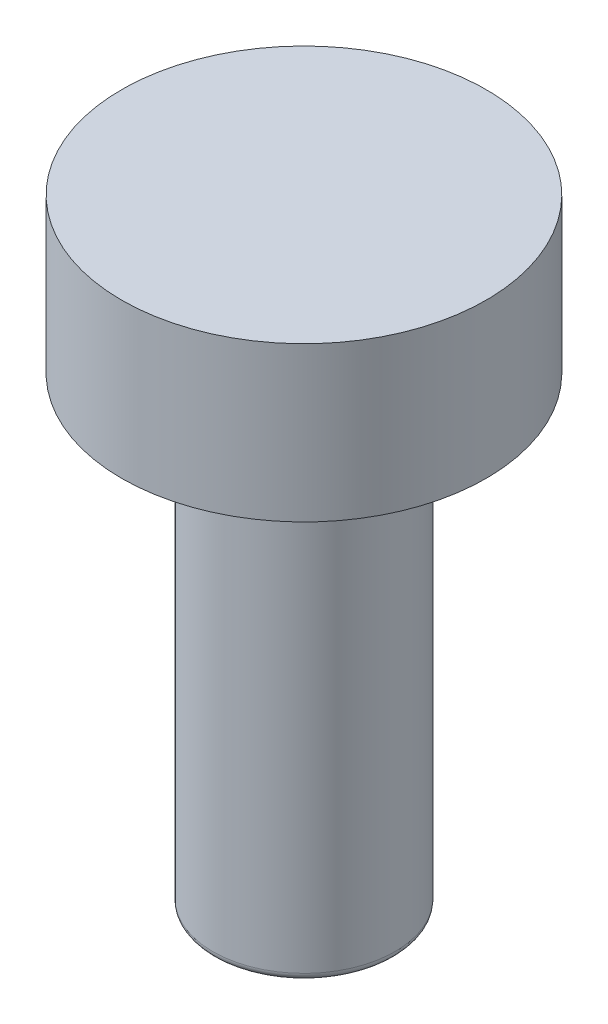
SolidWorks part; units mm, degrees
ref_plane "Front Plane" through (0, 0, 0) normal (0, 0, 1) x (1, 0, 0)
ref_plane "Top Plane" through (0, 0, 0) normal (0, 1, 0) x (1, 0, 0)
ref_plane "Right Plane" through (0, 0, 0) normal (1, 0, 0) x (0, 0, -1)
sketch "Sketch1" plane through (0, 0, 0) normal (0, 1, 0) x (1, 0, 0)
  line L0 (-1.6583, 2.5) -> (1.6583, 2.5)
  arc A0 (-1.6583, 2.5) -> (1.6583, 2.5) centre (0, 0) ccw
  dimension "D1" = 6
  dimension "D2" = 2.5
extrude "Boss-Extrude1" add sketch "Sketch1" along normal blind 15.24
sketch "Sketch2" plane through (0, 15.24, 0) normal (0, 1, 0) x (1, 0, 0)
  circle A0 centre (0, 0) radius 6
extrude "Boss-Extrude2" add sketch "Sketch2" along normal blind 5.08
fillet "Fillet1" radius 0.254 1 edges at (0, 0, 3)
